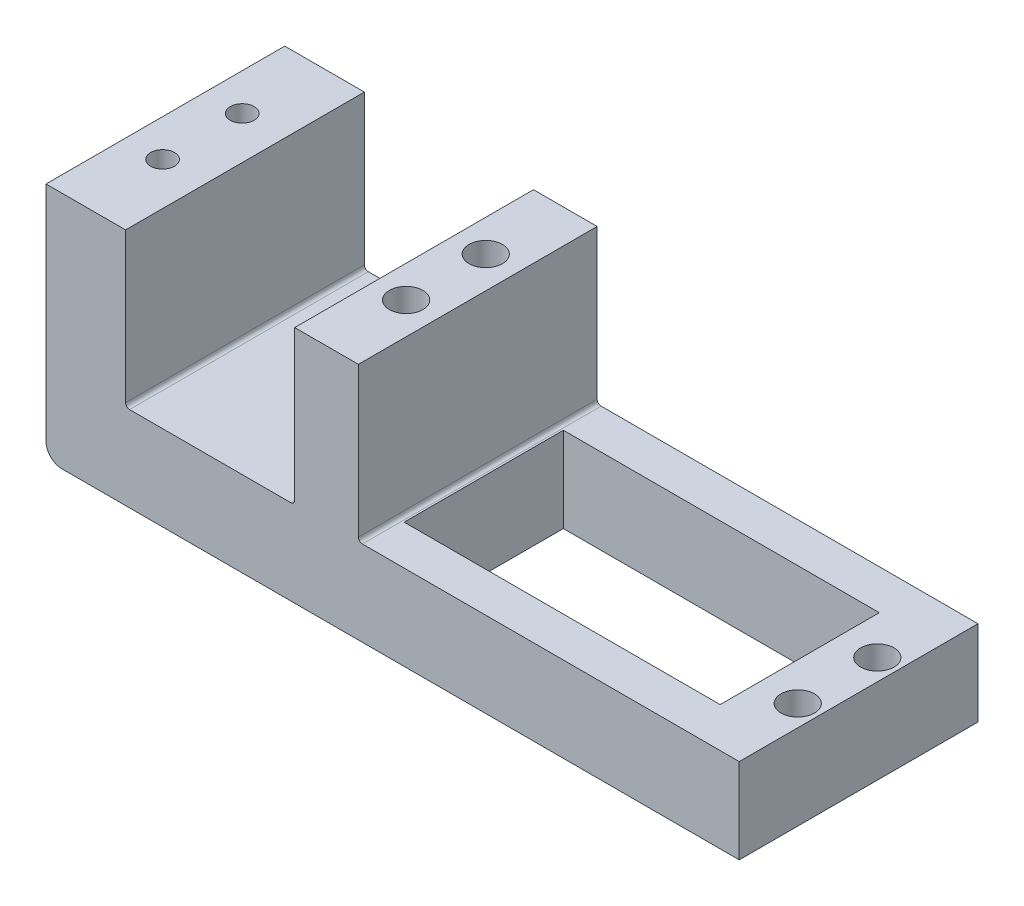
SolidWorks part; units mm, degrees
ref_plane "Front Plane" through (0, 0, 0) normal (0, 0, 1) x (1, 0, 0)
ref_plane "Top Plane" through (0, 0, 0) normal (0, 1, 0) x (1, 0, 0)
ref_plane "Right Plane" through (0, 0, 0) normal (1, 0, 0) x (0, 0, -1)
sketch "Sketch1" plane through (0, 0, 0) normal (0, 1, 0) x (1, 0, 0)
  line L0 (2.75, 10) -> (2.75, -10)
  line L1 (2.75, 10) -> (42.45, 10)
  line L7 (-27.25, 15) -> (49.85, 15)
  line L8 (2.75, -10) -> (42.45, -10)
  line L9 (42.45, 10) -> (42.45, -10)
  line L11 (-27.25, -15) -> (49.85, -15)
  line L15 (-27.25, 15) -> (-27.25, -15)
  line L16 (49.85, 15) -> (49.85, -15)
  point P0 (0, 0)
  point P6 (0, 0)
extrude "Boss-Extrude1" add sketch "Sketch1" along normal blind 10.7
sketch "Sketch4" plane through (-27.25, 0, 0) normal (-1, 0, 0) x (0, 0, 1)
  line L0 (15, 0) -> (-15, 0)
  line L1 (15, 0) -> (15, 30)
  line L2 (-15, 0) -> (-15, 30)
  line L3 (15, 30) -> (-15, 30)
extrude "Boss-Extrude3" add sketch "Sketch4" along normal blind 10
sketch "Sketch6" plane through (0, 0, 0) normal (0, -1, 0) x (-1, 0, 0)
  circle A0 centre (2, 5) radius 2.1
  circle A1 centre (2, -5) radius 2.1
  circle A2 centre (-47.2, 5) radius 2.1
  circle A3 centre (-47.2, -5) radius 2.1
extrude "Cut-Extrude2" cut sketch "Sketch6" against normal up to next
fillet "Fillet5" radius 2 1 edges at (-37.25, 0, 0)
fillet "Fillet6" radius 0.5 1 edges at (-27.25, 10.7, 0)
sketch "Sketch7" plane through (0, 0, 0) normal (0, -1, 0) x (-1, 0, 0)
  circle A0 centre (32.6, -5) radius 1.5
  circle A1 centre (32.6, 5) radius 1.5
extrude "Cut-Extrude3" cut sketch "Sketch7" against normal up to next
sketch "Sketch9" plane through (0, 10.7, 0) normal (0, 1, 0) x (1, 0, 0)
  line L1 (49.85, 15) -> (-26.75, 15) construction
  line L4 (-6, 15) -> (2, 15)
  line L5 (-6, 15) -> (-6, -15)
  line L6 (2, 15) -> (2, -15)
  line L7 (-6, -15) -> (2, -15)
  circle A0 centre (-2, 5) radius 2.1
  circle A1 centre (-2, -5) radius 2.1
extrude "Boss-Extrude4" add sketch "Sketch9" along normal blind 19.3
fillet "Fillet7" radius 0.5 2 edges at (2, 10.7, 0) (-6, 10.7, 0)
